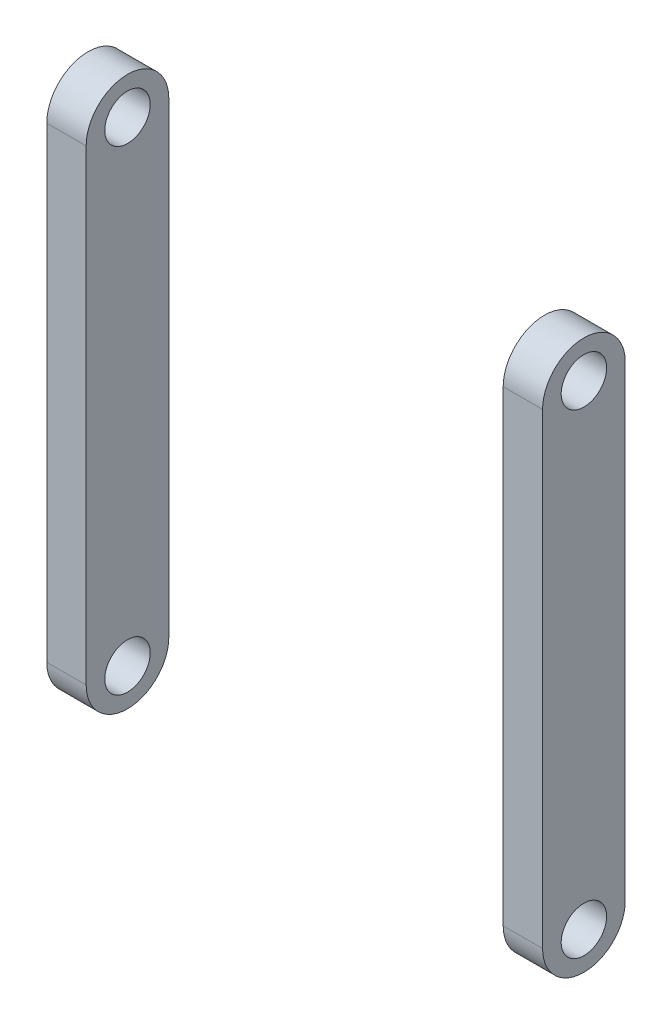
SolidWorks part; units mm, degrees
ref_plane "前视基准面" through (0, 0, 0) normal (0, 0, 1) x (1, 0, 0)
ref_plane "上视基准面" through (0, 0, 0) normal (0, 1, 0) x (1, 0, 0)
ref_plane "右视基准面" through (0, 0, 0) normal (1, 0, 0) x (0, 0, -1)
sketch "草图1" plane through (0, 0, 0) normal (0, 0, 1) x (1, 0, 0)
  line L0 (-12.25, -5) -> (-14.75, -5) construction
  line L1 (-24.5, -3) -> (-24.5, -17.6863) construction
  line L2 (-36.5, -3) -> (-34.5934, -3)
  line L3 (-12.5, -3) -> (-14.4066, -3)
  line L4 (-12.5, -3) -> (-12.5, -30)
  line L5 (-12.5, -30) -> (-14.4066, -30)
  line L6 (-14.4066, -3) -> (-14.4066, -30)
  line L7 (-34.5934, -3) -> (-34.5934, -30)
  line L8 (-36.5, -3) -> (-36.5, -30)
  line L9 (-36.5, -30) -> (-34.5934, -30)
  line L40 (1, 0) -> (-50, 0)
  line L41 (-50, 0) -> (-50, -3)
  line L42 (-50, -3) -> (-38.75, -3)
  line L43 (-38.75, -3) -> (-38.75, -7)
  line L44 (-38.75, -7) -> (-36.75, -7)
  line L45 (-36.75, -7) -> (-36.75, -3)
  line L46 (-36.75, -3) -> (-34.25, -3)
  line L47 (-34.25, -3) -> (-34.25, -7)
  line L48 (-34.25, -7) -> (-32.25, -7)
  line L49 (-32.25, -7) -> (-32.25, -3)
  line L50 (-32.25, -3) -> (-16.75, -3)
  line L51 (-16.75, -3) -> (-16.75, -7)
  line L52 (-16.75, -7) -> (-14.75, -7)
  line L53 (-14.75, -7) -> (-14.75, -3)
  line L54 (-14.75, -3) -> (-12.25, -3)
  line L55 (-12.25, -3) -> (-12.25, -7)
  line L56 (-12.25, -7) -> (-10.25, -7)
  line L57 (-10.25, -7) -> (-10.25, -3)
  line L58 (-10.25, -3) -> (1, -3)
  line L59 (1, -3) -> (1, 0)
  dimension "D2" = 0.25
  dimension "D3" = 27
extrude "凸台-拉伸1" add sketch "草图1" against normal blind 4 contours L3 L6 L5 L4 | L8 L9 L7 L2
sketch "草图2" plane through (-12.5, 0, 0) normal (1, 0, 0) x (0, 0, -1)
  line L0 (2, -30) -> (2, -3) construction
  line L4 (0, -3) -> (0, -30)
  line L5 (0, -30) -> (4, -30)
  line L6 (4, -30) -> (4, -3)
  line L7 (4, -3) -> (0, -3)
  line L8 (0, -3) -> (0, -30)
  line L9 (0, -30) -> (4, -30)
  line L10 (4, -30) -> (4, -3)
  line L11 (4, -3) -> (0, -3)
  circle A0 centre (2, -28) radius 1.1
  circle A2 centre (2, -5) radius 1.1
  circle A3 centre (2, -5.2) radius 2
  circle A5 centre (2, -27.8) radius 2
  line M5 (0, -3) -> (0, -30)
  line M6 (0, -30) -> (4, -30)
  line M7 (4, -30) -> (4, -3)
  line M8 (4, -3) -> (0, -3)
  dimension "D2" = 2.2
  dimension "D3" = 0.2
  dimension "D4" = 4
  dimension "D5" = 0.2
  dimension "D6" = 2
  dimension "D7" = 2
  dimension "D1" = 0
extrude "切除-拉伸6" cut sketch "草图2" against normal through all contours A3 L0 L11 M5 | L0 A3 M7 M8 | L0 A2 | A2 L0 | L0 A0 | A0 L0 | L0 L9 A5 M7 | L0 A5 M6 M5
